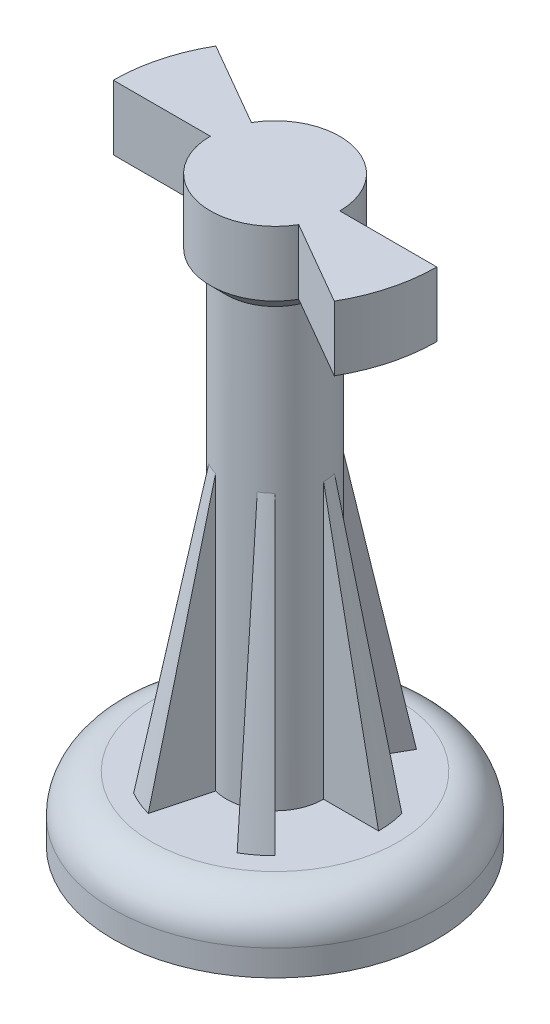
SolidWorks part; units mm, degrees
ref_plane "Front Plane" through (0, 0, 0) normal (0, 0, 1) x (1, 0, 0)
ref_plane "Top Plane" through (0, 0, 0) normal (0, 1, 0) x (1, 0, 0)
ref_plane "Right Plane" through (0, 0, 0) normal (1, 0, 0) x (0, 0, -1)
sketch "Sketch1" plane through (0, 0, 0) normal (0, 1, 0) x (1, 0, 0)
  circle A0 centre (0, 0) radius 12.5
  dimension "D1" = 25
extrude "Boss-Extrude1" add sketch "Sketch1" along normal blind 5 contours A0
sketch "Sketch2" plane through (0, 5, 0) normal (0, 1, 0) x (1, 0, 0)
  circle A0 centre (0, 0) radius 3.75
  dimension "D1" = 7.5
extrude "Boss-Extrude2" add sketch "Sketch2" along normal blind 40
sketch "Sketch3" plane through (0, 45, 0) normal (0, 1, 0) x (1, 0, 0)
  line L0 (3.75, 0) -> (12.5, 0)
  line L1 (3.2476, -1.875) -> (10.8253, -6.25)
  line L2 (-3.2476, 1.875) -> (-10.8253, 6.25)
  line L3 (-3.75, 0) -> (-12.5, 0)
  line L4 (3.2476, -1.875) -> (0, 0) construction
  line L5 (3.75, 0) -> (0, 0) construction
  arc A0 (-10.8253, 6.25) -> (-12.5, 0) centre (0, 0) ccw
  arc A1 (-3.75, 0) -> (3.2476, -1.875) centre (0, 0) ccw
  circle A2 centre (0, 0) radius 3.75 construction
  arc A3 (10.8253, -6.25) -> (12.5, 0) centre (0, 0) ccw
  arc A4 (3.75, 0) -> (-3.2476, 1.875) centre (0, 0) ccw
  dimension "D1" = 25
  dimension "D2" = 30
extrude "Boss-Extrude3" add sketch "Sketch3" against normal blind 5
sketch "Sketch6" plane through (0, 0, 0) normal (0, 0, 1) x (1, 0, 0)
  line L5 (0, 5) -> (0, 45)
  line L7 (0, 45) -> (8, 5)
  line L8 (12.5, 5) -> (-12.5, 5) construction
  line L9 (8, 5) -> (0, 5)
  line L10 (3.2476, 45) -> (-3.75, 45) construction
  point P2 (8.371, 5)
  dimension "D1" = 8
revolve "Revolve1" add sketch "Sketch6" angle 15 about L5
pattern_circular "CirPattern1" count 6 over 360 about axis through (0, 0, 0) along (0, 1, 0) of "Revolve1"
fillet "Fillet1" radius 3 1 edges at (0, 5, 12.5)
sketch "Sketch7" plane through (0, 45, 0) normal (0, 1, 0) x (1, 0, 0)
  circle A0 centre (0, 0) radius 5
  dimension "D1" = 10
extrude "Boss-Extrude4" add sketch "Sketch7" against normal blind 5
sketch "Sketch8" plane through (0, 40, 0) normal (0, -1, 0) x (-1, 0, 0)
  circle A0 centre (0, 0) radius 5
  arc A1 (4.3301, 2.5) -> (-5, 0) centre (0, 0) ccw construction
extrude "Boss-Extrude5" add sketch "Sketch8" along normal blind 5 draft 45
